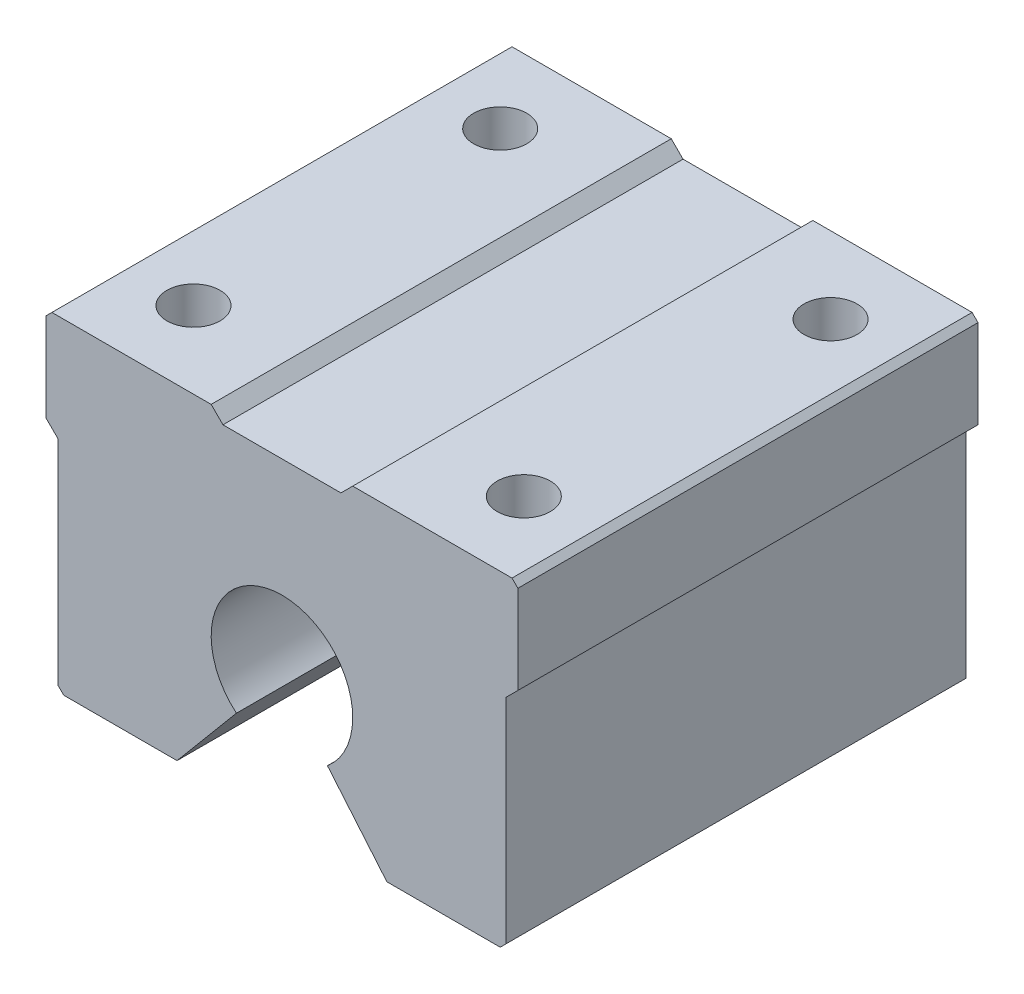
SolidWorks part; units mm, degrees
ref_plane "前视基准面" through (0, 0, 0) normal (0, 0, 1) x (1, 0, 0)
ref_plane "上视基准面" through (0, 0, 0) normal (0, 1, 0) x (1, 0, 0)
ref_plane "右视基准面" through (0, 0, 0) normal (1, 0, 0) x (0, 0, -1)
sketch "Sketch1" plane through (0, 0, 0) normal (0, 0, 1) x (1, 0, 0)
  line L0 (0, -8.8736) -> (0, 13.8) construction
  line L1 (-18.5, -13.8) -> (-8.8945, -13.8)
  line L2 (-20, 5.8) -> (-20, 13.3)
  line L3 (-19.5, 13.8) -> (-6, 13.8)
  line L4 (20, 5.8) -> (20, 13.3)
  line L5 (-20, -13.8) -> (20, 13.8) construction
  line L6 (-20, 13.8) -> (20, -13.8) construction
  line L7 (-3.8567, -7.7963) -> (-8.8945, -13.8)
  line L8 (3.8567, -7.7963) -> (8.8945, -13.8)
  line L9 (-20, 5.8) -> (-19, 4.8)
  line L10 (-19, 4.8) -> (-19, -13.3)
  line L11 (19, 4.8) -> (19, -13.3)
  line L12 (20, 5.8) -> (19, 4.8)
  line L13 (-20, 5.8) -> (-20, -13.8) construction
  line L14 (-20, -13.8) -> (-19, -13.8) construction
  line L15 (19, -13.8) -> (20, -13.8) construction
  line L16 (20, -13.8) -> (20, 5.8) construction
  line L17 (8.8945, -13.8) -> (18.5, -13.8)
  line L18 (3.8567, -7.7963) -> (0, -3.2) construction
  line L19 (0, -3.2) -> (-3.8567, -7.7963) construction
  line L20 (-6, 13.8) -> (-5, 12.8)
  line L21 (-5, 12.8) -> (5, 12.8)
  line L22 (5, 12.8) -> (6, 13.8)
  line L23 (6, 13.8) -> (19.5, 13.8)
  line L24 (19.5, 13.8) -> (20, 13.3)
  line L25 (-20, 13.3) -> (-19.5, 13.8)
  line L26 (-19, -13.3) -> (-18.5, -13.8)
  line L27 (19, -13.3) -> (18.5, -13.8)
  arc A0 (3.8567, -7.7963) -> (-3.8567, -7.7963) centre (0, -3.2) ccw
  point P0 (0, 0)
  point P23 (0, 12.8)
  point P24 (3.8567, 12.6936)
  point P25 (-4.4315, 13.0537)
  dimension "D1" = 12
  dimension "D2" = 40
  dimension "D3" = 40
  dimension "D4" = 40
  dimension "D5" = 27.6
  dimension "D6" = 17
  dimension "D7" = 135
  dimension "D8" = 1
  dimension "D9" = 5
  dimension "D10" = 8
  dimension "D11" = 135
  dimension "D12" = 1
extrude "Extrude1" add sketch "Sketch1" along normal blind 39
sketch "Sketch2" plane through (0, 13.8, 0) normal (0, 1, 0) x (1, 0, 0)
  line L0 (0, 0) -> (0, -39) construction
  line L1 (5, 0) -> (-5, 0) construction
  line L2 (5, -39) -> (-5, -39) construction
  line L4 (-14, -32.5) -> (14, -32.5) construction
  line L5 (-14, -32.5) -> (-14, -6.5) construction
  line L6 (-14, -6.5) -> (14, -6.5) construction
  line L7 (14, -32.5) -> (14, -6.5) construction
  line L8 (-14, -32.5) -> (14, -6.5) construction
  line L9 (-14, -6.5) -> (14, -32.5) construction
  circle A0 centre (-14, -6.5) radius 2.25
  circle A1 centre (-14, -32.5) radius 2.25
  circle A2 centre (14, -32.5) radius 2.25
  circle A3 centre (14, -6.5) radius 2.25
  point P6 (0, -19.5)
  dimension "D3" = 4.5
  dimension "D1" = 26
  dimension "D2" = 28
extrude "Extrude2" cut sketch "Sketch2" against normal blind 10
